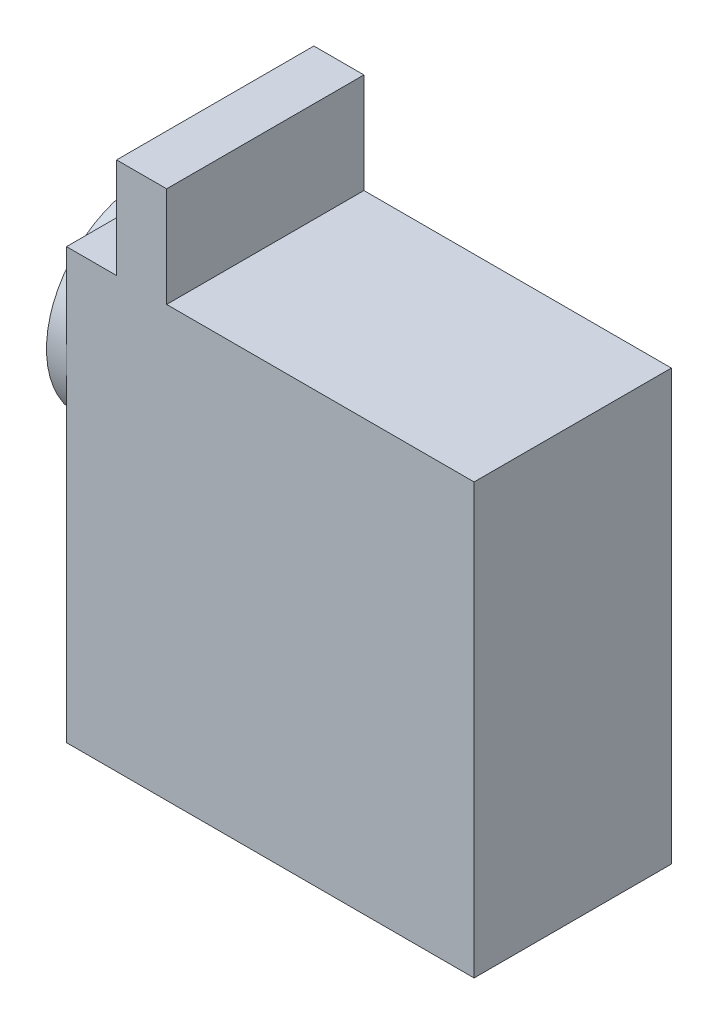
SolidWorks part; units mm, degrees
ref_plane "前基準面" through (0, 0, 0) normal (0, 0, 1) x (1, 0, 0)
ref_plane "上基準面" through (0, 0, 0) normal (0, 1, 0) x (1, 0, 0)
ref_plane "右基準面" through (0, 0, 0) normal (1, 0, 0) x (0, 0, -1)
sketch "草圖1" plane through (0, 0, 0) normal (0, 0, 1) x (1, 0, 0)
  line L1 (0, 0) -> (40.7, 0)
  line L2 (0, 0) -> (0, -42.9)
  line L3 (0, -42.9) -> (40.7, -42.9)
  line L4 (40.7, 0) -> (40.7, -42.9)
  dimension "D1" = 40.7
  dimension "D2" = 42.9
extrude "填料-伸長1" add sketch "草圖1" along normal blind 19.7
sketch "草圖2" plane through (0, 0, 0) normal (0, 1, 0) x (1, 0, 0)
  line L0 (40.7, 0) -> (0, 0) construction
  line L1 (5, 0) -> (10, 0)
  line L2 (5, 0) -> (5, -19.7)
  line L3 (5, -19.7) -> (10, -19.7)
  line L4 (10, 0) -> (10, -19.7)
  line L5 (40.7, -19.7) -> (0, -19.7) construction
  line L6 (0, -19.7) -> (0, 0) construction
  dimension "D1" = 5
  dimension "D2" = 5
extrude "填料-伸長2" add sketch "草圖2" along normal blind 10
sketch "草圖3" plane through (0, 0, 0) normal (-1, 0, 0) x (0, 0, 1)
  line L0 (19.7, 0) -> (0, 0) construction
  circle A0 centre (9.85, -9.85) radius 9.85
extrude "填料-伸長3" add sketch "草圖3" along normal blind 2
sketch "草圖4" plane through (-2, 0, 0) normal (-1, 0, 0) x (0, 0, 1)
  circle A0 centre (9.85, -9.85) radius 2.5
  dimension "D1" = 5
extrude "填料-伸長4" add sketch "草圖4" along normal blind 5
